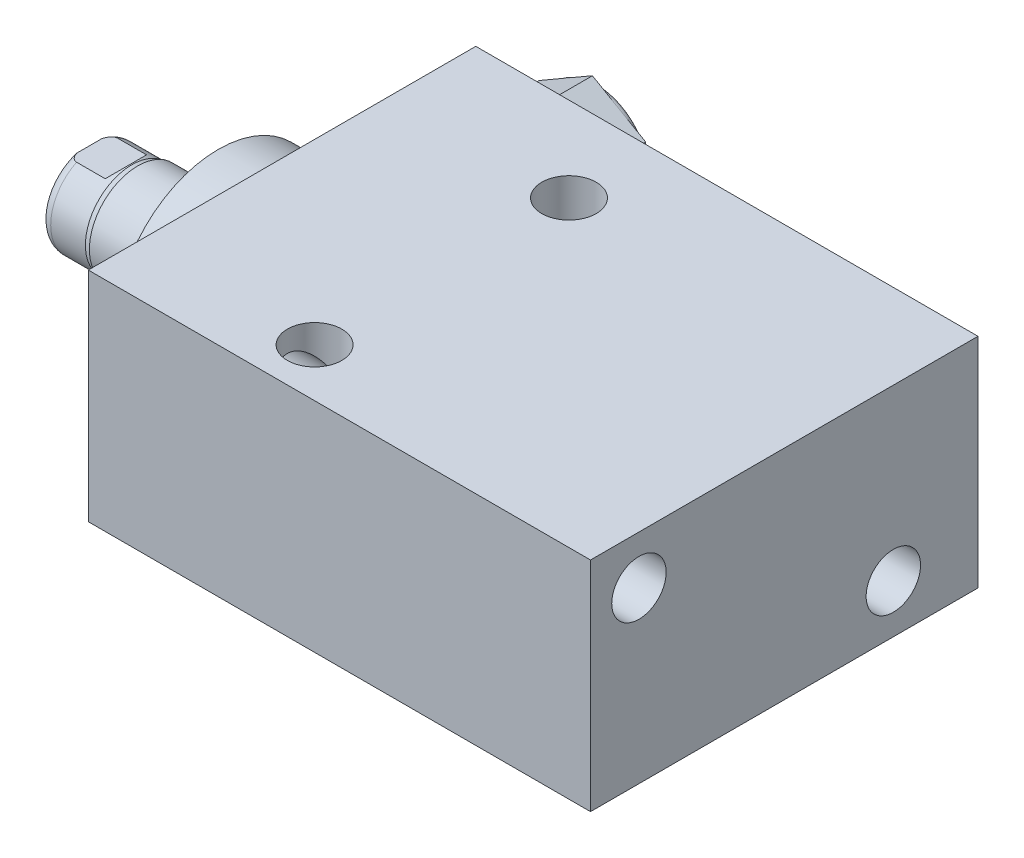
SolidWorks part; units mm, degrees
material "Alloy Steel"
ref_plane "Front Plane" through (0, 0, 0) normal (0, 0, 1) x (1, 0, 0)
ref_plane "Top Plane" through (0, 0, 0) normal (0, 1, 0) x (1, 0, 0)
ref_plane "Right Plane" through (0, 0, 0) normal (1, 0, 0) x (0, 0, -1)
ref_plane "Plane1" through (0, 0, 0) normal (1, 0, 0) x (0, 0, -1)
sketch "Sketch1" plane through (0, 0, 0) normal (1, 0, 0) x (0, 0, -1)
  line L0 (-23.0124, 14.2875) -> (27.7876, 14.2875)
  line L1 (27.7876, 14.2875) -> (27.7876, -14.2875)
  line L2 (27.7876, -14.2875) -> (-23.0124, -14.2875)
  line L3 (-23.0124, -14.2875) -> (-23.0124, 14.2875)
  line L4 (0, -24.4475) -> (0, 24.4475) construction
  dimension "D1" = 28.575
  dimension "D2" = 14.2875
  dimension "D3" = 50.8
  dimension "D4" = 23.0124
extrude "Extrude1" add sketch "Sketch1" along normal blind 65.8368
ref_plane "Plane12" through (0, 4.7625, 0) normal (0, 1, 0) x (-1, 0, 0)
sketch "S2D0002" plane through (0, 4.7625, 0) normal (0, 1, 0) x (-1, 0, 0)
  line L0 (-14.5415, -27.5336) -> (-18.161, -27.5336)
  line L1 (-14.5415, -27.5082) -> (-14.5415, -27.5336)
  line L2 (-14.5415, -27.5082) -> (-13.9446, -26.9113)
  line L3 (-13.9446, -26.9113) -> (-13.9446, -14.0716)
  line L4 (-13.9446, -14.0716) -> (-9.525, -14.0716)
  line L5 (-9.525, -14.0716) -> (-9.525, -27.7876)
  line L6 (-9.525, -19.1384) -> (-9.525, 0.6985) construction
  line L7 (0, -27.7876) -> (0, 23.0124) construction
  line L8 (-18.161, -27.7876) -> (-18.161, -27.5336)
  line L9 (-65.8368, -27.7876) -> (0, -27.7876) construction
  line L10 (-18.161, -27.7876) -> (-9.525, -27.7876)
  dimension "D1" = 13.716
  dimension "D2" = 9.525
  dimension "D3" = 8.8392
  dimension "D4" = 45
  dimension "D5" = 0.6223
  dimension "D6" = 10.033
  dimension "D7" = 0.0254
  dimension "D8" = 0.254
  dimension "D9" = 17.272
revolve "Cut-Revolve1" cut sketch "S2D0002" angle 360 about L6
pattern_linear "LPattern1" count 2 spacing 46.99 along (1, 0, 0) of "Cut-Revolve1"
sketch "Sketch5" plane through (0, 0, 0) normal (-1, 0, 0) x (0, 0, 1)
  circle A0 centre (0, 0) radius 13.5001
  dimension "D1" = 27.0002
extrude "Extrude2" add sketch "Sketch5" along normal blind 5.969
ref_plane "Plane5" through (0, 0, 0) normal (0, -1, 0) x (0, 0, 1)
sketch "Sketch6" plane through (0, 0, 0) normal (0, -1, 0) x (0, 0, 1)
  line L0 (0, 5.969) -> (-6.3373, 5.969)
  line L1 (-6.3373, 5.969) -> (-6.3373, 22.86)
  line L2 (-6.3373, 22.86) -> (0, 22.86)
  line L3 (0, 22.86) -> (0, 5.969)
  line L4 (0, -5.7546) -> (0, 21.1709) construction
  line L5 (13.5001, 5.969) -> (-13.5001, 5.969) construction
  line L6 (23.0124, -65.8368) -> (-27.7876, -65.8368) construction
  dimension "D1" = 88.6968
  dimension "D2" = 12.6746
revolve "Revolve1" add sketch "Sketch6" angle 360 about L4
ref_plane "Plane6" through (-18.5113, 3.2639, 0) normal (0, 0, 1) x (0, 1, 0)
sketch "S2D0001" plane through (-18.5113, 3.2639, 0) normal (0, 0, 1) x (0, 1, 0)
  line L0 (-0.7493, 2.9849) -> (-0.7493, -11.6533)
  line L1 (-3.2639, -13.1642) -> (-0.7493, -11.6533)
  line L2 (0.0381, 4.3487) -> (-3.2639, 4.3487)
  line L3 (-3.2639, 4.3487) -> (-3.2639, -13.1642)
  line L4 (-0.7493, 2.9849) -> (0.0381, 4.3487)
  line L5 (-3.2639, -18.5113) -> (-3.2639, 2.765) construction
  line L6 (3.0734, 4.3487) -> (-9.6012, 4.3487) construction
  dimension "D1" = 30
  dimension "D2" = 6.604
  dimension "D3" = 5.0292
  dimension "D4" = 16.002
  dimension "D5" = 59
revolve "Cut-Revolve4" cut sketch "S2D0001" angle 360 about L5
ref_plane "Plane7" through (0, 0, 0) normal (0, 1, 0) x (0, 0, -1)
sketch "Sketch8" plane through (0, 0, 0) normal (0, 1, 0) x (0, 0, -1)
  line L0 (-6.3373, 16.5354) -> (-6.096, 17.2974)
  line L1 (-6.096, 17.2974) -> (-6.096, 21.844)
  line L2 (0, 12.6594) -> (0, 20.8178) construction
  line L3 (-6.3373, 16.5354) -> (-6.3373, 22.86)
  line L4 (-5.7079, 22.86) -> (-6.3373, 22.86)
  line L5 (6.3373, 22.86) -> (-6.3373, 22.86) construction
  line L6 (-6.3373, 22.86) -> (-6.3373, 5.969) construction
  arc A0 (-5.7079, 22.86) -> (-6.096, 21.844) centre (-4.572, 21.844) ccw
  dimension "D2" = 1.524
  dimension "D1" = 12.192
  dimension "D3" = 1.016
  dimension "D4" = 0.762
  dimension "D5" = 5.5626
revolve "Cut-Revolve5" cut sketch "Sketch8" angle 360 about L2
ref_plane "Plane11" through (0, 0, 0) normal (0, 0, -1) x (0, -1, 0)
sketch "Sketch12" plane through (0, 0, 0) normal (0, 0, -1) x (0, -1, 0)
  line L0 (5.461, 22.86) -> (5.461, 18.0848)
  line L1 (5.461, 18.0848) -> (6.096, 17.4498)
  line L2 (-5.461, 22.86) -> (-5.461, 18.0848)
  line L3 (-5.461, 18.0848) -> (-6.096, 17.4498)
  line L4 (5.461, 22.86) -> (6.096, 22.86)
  line L5 (0, 13.7262) -> (0, 20.767) construction
  line L6 (-6.096, 17.4498) -> (-6.096, 22.86)
  line L8 (6.096, 17.2974) -> (6.096, 21.844) construction
  line L9 (6.096, 17.4498) -> (6.096, 22.86)
  line L10 (-5.461, 22.86) -> (-6.096, 22.86)
  line L12 (5.7079, 22.86) -> (-5.7079, 22.86) construction
  dimension "D1" = 10.922
  dimension "D2" = 4.7752
  dimension "D3" = 45
extrude "Cut-Extrude4" cut sketch "Sketch12" against normal mid plane 60.96
hole_wizard "Hole1" positions "Sketch15" profile "Sketch14" legacy end condition up to next
sketch "Sketch15" plane through (0, 0, 0) normal (-1, 0, 0) x (0, 0, 1)
  line L0 (0, 0) -> (-29.9914, 0) construction
  line L1 (0, 0) -> (0, 25.7648) construction
  point P0 (-16.6878, -7.9248)
  point P11 (16.6624, 7.9502)
  dimension "D1" = 7.9248
  dimension "D2" = 16.6878
  dimension "D3" = 15.875
  dimension "D4" = 33.3502
sketch "Sketch14" plane through (0, -7.9248, -16.6878) normal (0, 1, 0) x (0, 0, 1)
  line L0 (0, 0) -> (0, 65.8368)
  line L1 (0, 65.8368) -> (3.5685, 65.8368)
  line L2 (3.5685, 65.8368) -> (3.5685, 0)
  line L3 (3.5685, 0) -> (0, 0)
  line L4 (0, 110) -> (0, -10) construction
  dimension "Diameter" = 7.137
  dimension "Depth" = 65.8368
hole_wizard "Hole2" positions "Sketch17" profile "Sketch16" legacy
sketch "Sketch17" plane through (0, 14.2875, 0) normal (0, 1, 0) x (-1, 0, 0)
  line L0 (0, 0) -> (-59.3363, 0) construction
  line L1 (0, -27.7876) -> (0, 23.0124) construction
  point P0 (-23.3172, -16.6878)
  point P9 (-23.3172, 16.6624)
  dimension "D1" = 33.3502
  dimension "D2" = 23.3172
  dimension "D3" = 16.6878
sketch "Sketch16" plane through (23.3172, 14.2875, -16.6878) normal (1, 0, 0) x (0, 0, 1)
  line L0 (0, 0) -> (0, 28.575)
  line L1 (0, 28.575) -> (3.5685, 28.575)
  line L2 (3.5685, 28.575) -> (3.5685, 0)
  line L3 (3.5685, 0) -> (0, 0)
  line L4 (0, 110) -> (0, -10) construction
  dimension "Diameter" = 7.137
  dimension "Depth" = 28.575
sketch "Sketch18" plane through (0, 0, -27.5336) normal (0, 0, -1) x (-1, 0, 0)
  line L1 (-2.54, 8.7953) -> (-9.525, 12.8281)
  line L2 (-9.525, 12.8281) -> (-16.51, 8.7953)
  line L3 (-16.51, 8.7953) -> (-16.51, 0.7297)
  line L4 (-16.51, 0.7297) -> (-9.525, -3.3031)
  line L5 (-9.525, -3.3031) -> (-2.54, 0.7297)
  line L6 (-2.54, 0.7297) -> (-2.54, 8.7953)
  circle A0 centre (-9.525, 4.7625) radius 6.985 construction
  dimension "D1" = 13.97
extrude "Extrude3" add sketch "Sketch18" along normal blind 6.78
sketch "Sketch19" plane through (0, 4.7625, 0) normal (0, 1, 0) x (-1, 0, 0)
  line L0 (-9.525, -18.5103) -> (-9.525, -44.3941) construction
  line L1 (-9.525, -14.0716) -> (-9.525, -26.9113) construction
  line L2 (-9.525, -34.3136) -> (-16.51, -34.3136) construction
  line L3 (-16.51, -34.3136) -> (-16.51, -27.5336) construction
  line L4 (-15.748, -34.3136) -> (-15.748, -36.7266)
  line L5 (-15.748, -36.7266) -> (-18.923, -36.7266)
  line L6 (-18.923, -36.7266) -> (-18.923, -33.5516)
  line L7 (-18.923, -33.5516) -> (-16.51, -33.5516)
  arc A0 (-16.51, -33.5516) -> (-15.748, -34.3136) centre (-15.748, -33.5516) ccw
  dimension "D1" = 0.762
  dimension "D2" = 3.175
  dimension "D3" = 3.175
revolve "Cut-Revolve6" cut sketch "Sketch19" angle 360 about L0
